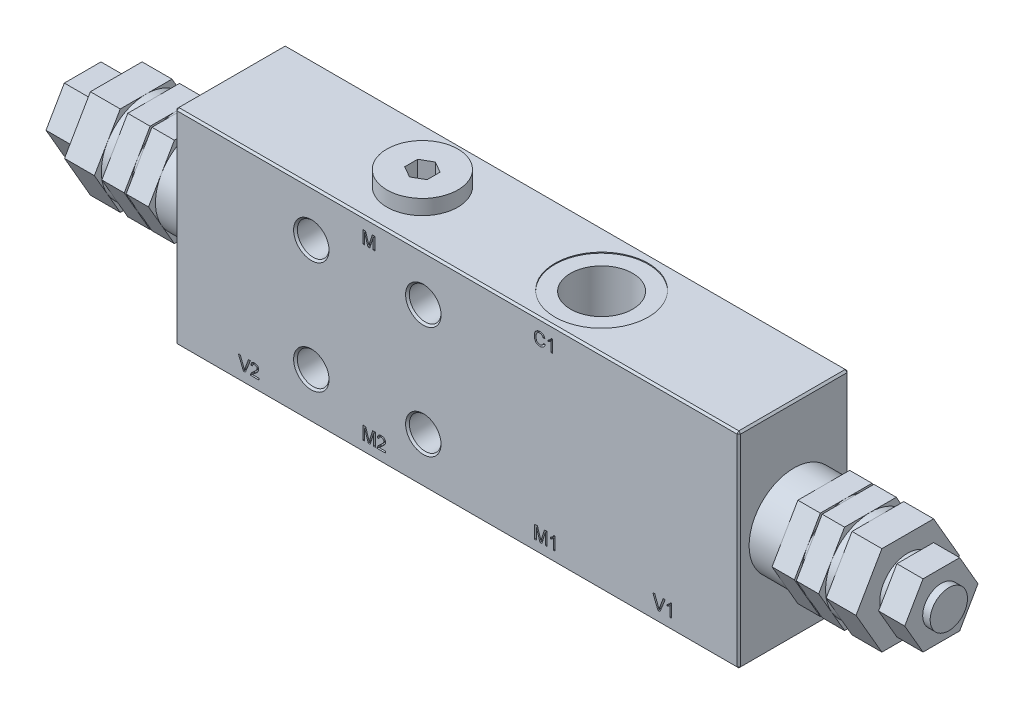
SolidWorks part; units mm, degrees
ref_plane "Front" through (0, 0, 0) normal (0, 0, 1) x (1, 0, 0)
ref_plane "Top" through (0, 0, 0) normal (0, 1, 0) x (1, 0, 0)
ref_plane "Right" through (0, 0, 0) normal (1, 0, 0) x (0, 0, -1)
sketch "Sketch1" plane through (0, 0, 0) normal (0, 0, 1) x (1, 0, 0)
  line L0 (0, 0) -> (151, 0)
  line L1 (0, 0) -> (0, 55)
  line L2 (151, 55) -> (0, 55)
  line L3 (151, 55) -> (151, 0)
  circle A0 centre (36.5, 42.5) radius 4.25
  circle A1 centre (66.5, 42.5) radius 4.25
  circle A2 centre (36.5, 12.5) radius 4.25
  circle A3 centre (66.5, 12.5) radius 4.25
  dimension "D6" = 8.5
  dimension "D1" = 55
  dimension "D2" = 12.5
  dimension "D3" = 30
  dimension "D4" = 30
  dimension "D5" = 36.5
  dimension "D7" = 151
extrude "Base-Extrude" add sketch "Sketch1" against normal blind 29.5
chamfer "Chamfer1" distance 0.5 angle 45 20 edges at (151, 27.5, -29.5) (40.75, 42.5, -29.5) (40.75, 42.5, 0) (75.5, 0, -29.5) (70.75, 42.5, -29.5) (70.75, 42.5, 0) (40.75, 12.5, -29.5) (40.75, 12.5, 0) (70.75, 12.5, -29.5) (70.75, 12.5, 0) (0, 27.5, -29.5) (75.5, 0, 0) (151, 27.5, 0) (75.5, 55, 0) (0, 27.5, 0) (75.5, 55, -29.5) (0, 0, -14.75) (151, 0, -14.75) (151, 55, -14.75) (0, 55, -14.75)
sketch "Sketch5" plane through (0, 0, -29.5) normal (0, 0, -1) x (-1, 0, 0)
  line L0 (0, 0) -> (0, 55) construction
  line L1 (0, 0) -> (-151, 0) construction
  circle A0 centre (-51.5, 27.5) radius 4.5
  dimension "D2" = 9
  dimension "D1" = 51.5
  dimension "D3" = 27.5
extrude "Cut-Extrude4" cut sketch "Sketch5" against normal blind 20
hole_wizard "Hole1" positions "Sketch7" profile "Sketch6" legacy
sketch "Sketch7" plane through (0, 55, 0) normal (0, 1, 0) x (-1, 0, 0)
  line L0 (-151, -29) -> (-151, -0.5) construction
  line L1 (-0.5, -29.5) -> (-150.5, -29.5) construction
  point P0 (-99.5, -14.75)
  dimension "D1" = 51.5
  dimension "D2" = 14.75
sketch "Sketch6" plane through (99.5, 55, -14.75) normal (1, 0, 0) x (0, 0, 1)
  line L0 (0, 0) -> (0, 20)
  line L1 (0, 20) -> (8.331, 20)
  line L2 (8.331, 20) -> (8.331, 0.25)
  line L3 (8.331, 0.25) -> (12.5, 0.25)
  line L4 (12.5, 0.25) -> (12.5, 0)
  line L5 (12.5, 0) -> (0, 0)
  line L6 (0, 110) -> (0, -10) construction
  dimension "Diameter" = 16.662
  dimension "Depth" = 20
  dimension "C-Bore Diameter" = 25
  dimension "C-Bore Depth" = 0.25
sketch "Sketch8" plane through (0, 55, 0) normal (0, 1, 0) x (-1, 0, 0)
  line L3 (-0.5, -29.5) -> (-150.5, -29.5) construction
  circle A0 centre (-51.5, -14.75) radius 9.5
  circle A1 centre (-99.5, -14.75) radius 8.331 construction
  dimension "D1" = 48
  dimension "D2" = 19
  dimension "D3" = 14.75
extrude "Boss-Extrude1" add sketch "Sketch8" along normal blind 4
sketch "Sketch9" plane through (0, 59, 0) normal (0, 1, 0) x (-1, 0, 0)
  line L1 (-51.5, -18.2141) -> (-48.5, -16.4821)
  line L2 (-48.5, -16.4821) -> (-48.5, -13.0179)
  line L3 (-48.5, -13.0179) -> (-51.5, -11.2859)
  line L4 (-51.5, -11.2859) -> (-54.5, -13.0179)
  line L5 (-54.5, -13.0179) -> (-54.5, -16.4821)
  line L6 (-54.5, -16.4821) -> (-51.5, -18.2141)
  circle A0 centre (-51.5, -14.75) radius 3 construction
  circle A1 centre (-51.5, -14.75) radius 9.5 construction
  dimension "D1" = 6
extrude "Cut-Extrude5" cut sketch "Sketch9" against normal blind 10
hole_wizard "Hole2" positions "Sketch12" profile "Sketch11" legacy
sketch "Sketch12" plane through (0, 0, 0) normal (0, -1, 0) x (1, 0, 0)
  line L0 (0.5, 0) -> (150.5, 0) construction
  line L1 (151, -0.5) -> (151, -29) construction
  point P0 (131, -14.75)
  dimension "D1" = 14.75
  dimension "D2" = 20
sketch "Sketch11" plane through (131, 0, -14.75) normal (1, 0, 0) x (0, 0, -1)
  line L0 (0, 0) -> (0, 20)
  line L1 (0, 20) -> (8.331, 20)
  line L2 (8.331, 20) -> (8.331, 0.25)
  line L3 (8.331, 0.25) -> (12.5, 0.25)
  line L4 (12.5, 0.25) -> (12.5, 0)
  line L5 (12.5, 0) -> (0, 0)
  line L6 (0, 110) -> (0, -10) construction
  dimension "Diameter" = 16.662
  dimension "Depth" = 20
  dimension "C-Bore Diameter" = 25
  dimension "C-Bore Depth" = 0.25
pattern_linear "LPattern1" count 2 spacing 111 along (-1, 0, 0) of "Hole2"
sketch "Sketch13" plane through (0, 0, 0) normal (0, -1, 0) x (1, 0, 0)
  line L2 (151, -0.5) -> (151, -29) construction
  line L3 (0.5, -29.5) -> (150.5, -29.5) construction
  circle A0 centre (98, -14.75) radius 9.5
  circle A1 centre (52, -14.75) radius 9.5 construction
  dimension "D1" = 19
  dimension "D2" = 53
  dimension "D3" = 46
  dimension "D4" = 14.75
extrude "Boss-Extrude2" add sketch "Sketch13" along normal blind 4
sketch "Sketch14" plane through (0, -4, 0) normal (0, -1, 0) x (1, 0, 0)
  line L1 (98, -11.2859) -> (95, -13.0179)
  line L2 (95, -13.0179) -> (95, -16.4821)
  line L3 (95, -16.4821) -> (98, -18.2141)
  line L4 (98, -18.2141) -> (101, -16.4821)
  line L5 (101, -16.4821) -> (101, -13.0179)
  line L6 (101, -13.0179) -> (98, -11.2859)
  line L8 (52, -11.2859) -> (49, -13.0179) construction
  line L9 (49, -13.0179) -> (49, -16.4821) construction
  line L10 (49, -16.4821) -> (52, -18.2141) construction
  line L11 (52, -18.2141) -> (55, -16.4821) construction
  line L12 (55, -16.4821) -> (55, -13.0179) construction
  line L13 (55, -13.0179) -> (52, -11.2859) construction
  circle A0 centre (98, -14.75) radius 3 construction
  circle A1 centre (52, -14.75) radius 3 construction
  circle A3 centre (98, -14.75) radius 9.5 construction
  dimension "D1" = 6
  dimension "D2" = 6
extrude "Cut-Extrude6" cut sketch "Sketch14" against normal blind 10
sketch "Sketch43" plane through (0, 0, 0) normal (0, -1, 0) x (1, 0, 0)
  circle A0 centre (52, -14.75) radius 9.5 construction
  circle A1 centre (52, -14.75) radius 9.5
extrude "Extrude1" add sketch "Sketch43" along normal up to surface (4 mm away) up to face at (98, -4, -14.75)
sketch "Sketch44" plane through (0, -4, 0) normal (0, -1, 0) x (1, 0, 0)
  line L0 (49, -13.0179) -> (49, -16.4821) construction
  line L1 (49, -16.4821) -> (52, -18.2141) construction
  line L2 (52, -18.2141) -> (55, -16.4821) construction
  line L3 (55, -16.4821) -> (55, -13.0179) construction
  line L4 (55, -13.0179) -> (52, -11.2859) construction
  line L5 (52, -11.2859) -> (49, -13.0179) construction
  line L6 (49, -13.0179) -> (49, -16.4821)
  line L7 (49, -16.4821) -> (52, -18.2141)
  line L8 (52, -18.2141) -> (55, -16.4821)
  line L9 (55, -16.4821) -> (55, -13.0179)
  line L10 (55, -13.0179) -> (52, -11.2859)
  line L11 (52, -11.2859) -> (49, -13.0179)
extrude "Cut-Extrude13" cut sketch "Sketch44" against normal up to surface (10 mm away) up to face at (98, 6, -14.75)
sketch "Sketch15" plane through (151, 0, 0) normal (1, 0, 0) x (0, 0, -1)
  line L0 (9.5, 27.5) -> (29.5, 27.5) construction
  line L3 (0, 0.5) -> (0, 54.5) construction
  circle A0 centre (14.75, 27.5) radius 12
  dimension "D1" = 24
  dimension "D2" = 14.75
extrude "Boss-Extrude3" add sketch "Sketch15" along normal blind 8
sketch "Sketch16" plane through (159, 0, 0) normal (1, 0, 0) x (0, 0, -1)
  line L0 (9.5, 27.5) -> (29.5, 27.5) construction
  line L1 (21.6782, 39.5) -> (7.8218, 39.5)
  line L2 (7.8218, 39.5) -> (0.8936, 27.5)
  line L3 (0.8936, 27.5) -> (7.8218, 15.5)
  line L4 (7.8218, 15.5) -> (21.6782, 15.5)
  line L5 (21.6782, 15.5) -> (28.6064, 27.5)
  line L6 (28.6064, 27.5) -> (21.6782, 39.5)
  circle A0 centre (14.75, 27.5) radius 12 construction
  circle A1 centre (14.75, 27.5) radius 12 construction
  dimension "D1" = 24
extrude "Boss-Extrude4" add sketch "Sketch16" along normal blind 6
sketch "Sketch17" plane through (165, 0, 0) normal (1, 0, 0) x (0, 0, -1)
  circle A0 centre (14.75, 27.5) radius 12
  circle A1 centre (14.75, 27.5) radius 12 construction
  dimension "D1" = 24
extrude "Boss-Extrude5" add sketch "Sketch17" along normal blind 0.5
sketch "Sketch18" plane through (165.5, 0, 0) normal (1, 0, 0) x (0, 0, -1)
  line L0 (9.5, 27.5) -> (29.5, 27.5) construction
  line L1 (0.8936, 27.5) -> (7.8218, 15.5)
  line L2 (7.8218, 15.5) -> (21.6782, 15.5)
  line L3 (21.6782, 15.5) -> (28.6064, 27.5)
  line L4 (28.6064, 27.5) -> (21.6782, 39.5)
  line L5 (21.6782, 39.5) -> (7.8218, 39.5)
  line L6 (7.8218, 39.5) -> (0.8936, 27.5)
  circle A0 centre (14.75, 27.5) radius 12 construction
  circle A1 centre (14.75, 27.5) radius 12 construction
  dimension "D1" = 24
extrude "Boss-Extrude6" add sketch "Sketch18" along normal blind 6
sketch "Sketch19" plane through (171.5, 0, 0) normal (1, 0, 0) x (0, 0, -1)
  circle A0 centre (14.75, 27.5) radius 12
  dimension "D1" = 24
extrude "Boss-Extrude7" add sketch "Sketch19" along normal blind 2
sketch "Sketch20" plane through (173.5, 0, 0) normal (1, 0, 0) x (0, 0, -1)
  line L1 (0.8936, 27.5) -> (7.8218, 15.5)
  line L2 (7.8218, 15.5) -> (21.6782, 15.5)
  line L3 (21.6782, 15.5) -> (28.6064, 27.5)
  line L4 (28.6064, 27.5) -> (21.6782, 39.5)
  line L5 (21.6782, 39.5) -> (7.8218, 39.5)
  line L6 (7.8218, 39.5) -> (0.8936, 27.5)
  circle A0 centre (14.75, 27.5) radius 12 construction
  dimension "D1" = 24
extrude "Boss-Extrude8" add sketch "Sketch20" along normal blind 8
sketch "Sketch21" plane through (181.5, 0, 0) normal (1, 0, 0) x (0, 0, -1)
  circle A0 centre (14.75, 27.5) radius 7.5
  dimension "D1" = 15
extrude "Boss-Extrude9" add sketch "Sketch21" along normal blind 2
sketch "Sketch22" plane through (183.5, 0, 0) normal (1, 0, 0) x (0, 0, -1)
  line L1 (4.935, 27.5) -> (9.8425, 19)
  line L2 (9.8425, 19) -> (19.6575, 19)
  line L3 (19.6575, 19) -> (24.565, 27.5)
  line L4 (24.565, 27.5) -> (19.6575, 36)
  line L5 (19.6575, 36) -> (9.8425, 36)
  line L6 (9.8425, 36) -> (4.935, 27.5)
  circle A0 centre (14.75, 27.5) radius 8.5 construction
  dimension "D1" = 17
extrude "Boss-Extrude10" add sketch "Sketch22" along normal blind 7
sketch "Sketch23" plane through (190.5, 0, 0) normal (1, 0, 0) x (0, 0, -1)
  circle A0 centre (14.75, 27.5) radius 5
  dimension "D1" = 10
extrude "Boss-Extrude11" add sketch "Sketch23" along normal blind 2
sketch "Sketch24" plane through (0, 0, 0) normal (-1, 0, 0) x (0, 0, 1)
  line L0 (-9.5, 27.5) -> (-29.5, 27.5) construction
  line L1 (0, 54.5) -> (0, 0.5) construction
  circle A0 centre (-14.75, 27.5) radius 12
  dimension "D1" = 24
  dimension "D2" = 14.75
extrude "Boss-Extrude12" add sketch "Sketch24" along normal blind 8
sketch "Sketch25" plane through (-8, 0, 0) normal (-1, 0, 0) x (0, 0, 1)
  line L0 (-9.5, 27.5) -> (-29.5, 27.5) construction
  line L1 (-0.8936, 27.5) -> (-7.8218, 39.5)
  line L2 (-7.8218, 39.5) -> (-21.6782, 39.5)
  line L3 (-21.6782, 39.5) -> (-28.6064, 27.5)
  line L4 (-28.6064, 27.5) -> (-21.6782, 15.5)
  line L5 (-21.6782, 15.5) -> (-7.8218, 15.5)
  line L6 (-7.8218, 15.5) -> (-0.8936, 27.5)
  circle A0 centre (-14.75, 27.5) radius 12 construction
  circle A1 centre (-14.75, 27.5) radius 12 construction
  dimension "D1" = 24
extrude "Boss-Extrude13" add sketch "Sketch25" along normal blind 6
sketch "Sketch26" plane through (-14, 0, 0) normal (-1, 0, 0) x (0, 0, 1)
  circle A0 centre (-14.75, 27.5) radius 12
  dimension "D1" = 24
extrude "Boss-Extrude14" add sketch "Sketch26" along normal blind 0.5
sketch "Sketch27" plane through (-14.5, 0, 0) normal (-1, 0, 0) x (0, 0, 1)
  line L1 (-0.8936, 27.5) -> (-7.8218, 39.5)
  line L2 (-7.8218, 39.5) -> (-21.6782, 39.5)
  line L3 (-21.6782, 39.5) -> (-28.6064, 27.5)
  line L4 (-28.6064, 27.5) -> (-21.6782, 15.5)
  line L5 (-21.6782, 15.5) -> (-7.8218, 15.5)
  line L6 (-7.8218, 15.5) -> (-0.8936, 27.5)
  circle A0 centre (-14.75, 27.5) radius 12 construction
  dimension "D1" = 24
extrude "Boss-Extrude15" add sketch "Sketch27" along normal blind 6
sketch "Sketch28" plane through (-20.5, 0, 0) normal (-1, 0, 0) x (0, 0, 1)
  line L0 (-9.5, 27.5) -> (-29.5, 27.5) construction
  circle A0 centre (-14.75, 27.5) radius 12
  circle A1 centre (-14.75, 27.5) radius 12 construction
  dimension "D1" = 24
extrude "Boss-Extrude16" add sketch "Sketch28" along normal blind 2
sketch "Sketch29" plane through (-22.5, 0, 0) normal (-1, 0, 0) x (0, 0, 1)
  line L1 (-0.8936, 27.5) -> (-7.8218, 39.5)
  line L2 (-7.8218, 39.5) -> (-21.6782, 39.5)
  line L3 (-21.6782, 39.5) -> (-28.6064, 27.5)
  line L4 (-28.6064, 27.5) -> (-21.6782, 15.5)
  line L5 (-21.6782, 15.5) -> (-7.8218, 15.5)
  line L6 (-7.8218, 15.5) -> (-0.8936, 27.5)
  circle A0 centre (-14.75, 27.5) radius 12 construction
  dimension "D1" = 24
extrude "Boss-Extrude17" add sketch "Sketch29" along normal blind 8
sketch "Sketch30" plane through (-30.5, 0, 0) normal (-1, 0, 0) x (0, 0, 1)
  circle A0 centre (-14.75, 27.5) radius 7.5
  dimension "D1" = 15
extrude "Boss-Extrude18" add sketch "Sketch30" along normal blind 2
sketch "Sketch31" plane through (-32.5, 0, 0) normal (-1, 0, 0) x (0, 0, 1)
  line L1 (-4.935, 27.5) -> (-9.8425, 36)
  line L2 (-9.8425, 36) -> (-19.6575, 36)
  line L3 (-19.6575, 36) -> (-24.565, 27.5)
  line L4 (-24.565, 27.5) -> (-19.6575, 19)
  line L5 (-19.6575, 19) -> (-9.8425, 19)
  line L6 (-9.8425, 19) -> (-4.935, 27.5)
  circle A0 centre (-14.75, 27.5) radius 8.5 construction
  dimension "D1" = 17
extrude "Boss-Extrude19" add sketch "Sketch31" along normal blind 7
sketch "Sketch32" plane through (-39.5, 0, 0) normal (-1, 0, 0) x (0, 0, 1)
  line L0 (-14.75, 54.75) -> (-14.75, 55) construction
  circle A0 centre (-14.75, 27.5) radius 5
  circle A2 centre (-14.75, 27.5) radius 12 construction
  dimension "D1" = 10
extrude "Boss-Extrude20" add sketch "Sketch32" along normal blind 2
sketch "Sketch33" plane through (0, 0, 0) normal (0, 0, 1) x (1, 0, 0)
  line L0 (150.5, 0) -> (0.5, 0) construction
  line L1 (151, 54.5) -> (151, 0.5) construction
  text T0 "V1" font "Arial" height 3.5
  dimension "D1" = 3
  dimension "D2" = 23
extrude "Cut-Extrude7" cut sketch "Sketch33" against normal blind 1
sketch "Sketch34" plane through (0, 0, 0) normal (0, 0, 1) x (1, 0, 0)
  line L0 (0, 0.5) -> (0, 54.5) construction
  line L1 (150.5, 0) -> (0.5, 0) construction
  text T0 "V2" font "Arial" height 3.5
  dimension "D1" = 17
  dimension "D2" = 3
extrude "Cut-Extrude8" cut sketch "Sketch34" against normal blind 1
sketch "Sketch35" plane through (0, 0, 0) normal (0, 0, 1) x (1, 0, 0)
  line L1 (151, 54.5) -> (151, 0.5) construction
  line L2 (0.5, 55) -> (150.5, 55) construction
  text T0 "C1" font "Arial" height 3.5
  dimension "D1" = 55
  dimension "D2" = 6.5
extrude "Cut-Extrude9" cut sketch "Sketch35" against normal blind 1
sketch "Sketch36" plane through (0, 0, 0) normal (0, 0, 1) x (1, 0, 0)
  line L0 (0.5, 55) -> (150.5, 55) construction
  line L1 (0, 0.5) -> (0, 54.5) construction
  text T0 "M" font "Arial" height 3.5
  dimension "D1" = 6.5
  dimension "D2" = 50
extrude "Cut-Extrude10" cut sketch "Sketch36" against normal blind 1
sketch "Sketch37" plane through (0, 0, 0) normal (0, 0, 1) x (1, 0, 0)
  line L0 (150.5, 0) -> (0.5, 0) construction
  line L1 (0, 0.5) -> (0, 54.5) construction
  text T0 "M2" font "Arial" height 3.5
  dimension "D1" = 3
  dimension "D2" = 50
extrude "Cut-Extrude11" cut sketch "Sketch37" against normal blind 1
sketch "Sketch38" plane through (0, 0, 0) normal (0, 0, 1) x (1, 0, 0)
  line L0 (150.5, 0) -> (0.5, 0) construction
  line L1 (151, 54.5) -> (151, 0.5) construction
  text T0 "M1" font "Arial" height 3.5
  dimension "D1" = 3
  dimension "D2" = 55
extrude "Cut-Extrude12" cut sketch "Sketch38" against normal blind 1
hole_wizard "Hole3" [suppressed] positions "Sketch40" profile "Sketch39" legacy
sketch "Sketch40" plane through (0, 55, 0) normal (0, 1, 0) x (-1, 0, 0)
  line L0 (-150.5, 0) -> (-0.5, 0) construction
  circle A0 centre (-99.5, -14.75) radius 8.331 construction
  point P0 (-51.5, -14.75)
  dimension "D2" = 48
  dimension "D1" = 14.75
sketch "Sketch39" plane through (51.5, 55, -14.75) normal (1, 0, 0) x (0, 0, 1)
  line L0 (0, 0) -> (0, 20)
  line L1 (0, 20) -> (6.5785, 20)
  line L2 (6.5785, 20) -> (6.5785, 0.25)
  line L3 (6.5785, 0.25) -> (11, 0.25)
  line L4 (11, 0.25) -> (11, 0)
  line L5 (11, 0) -> (0, 0)
  line L6 (0, 110) -> (0, -10) construction
  dimension "Diameter" = 13.157
  dimension "Depth" = 20
  dimension "C-Bore Diameter" = 22
  dimension "C-Bore Depth" = 0.25
hole_wizard "Hole4" [suppressed] positions "Sketch42" profile "Sketch41" legacy
sketch "Sketch42" plane through (0, 0, 0) normal (0, -1, 0) x (1, 0, 0)
  line L0 (0.5, 0) -> (150.5, 0) construction
  line L1 (151, -0.5) -> (151, -29) construction
  point P0 (52, -14.75)
  dimension "D1" = 14.75
  dimension "D2" = 53
sketch "Sketch41" plane through (52, 0, -14.75) normal (1, 0, 0) x (0, 0, -1)
  line L0 (0, 0) -> (0, 20)
  line L1 (0, 20) -> (6.5785, 20)
  line L2 (6.5785, 20) -> (6.5785, 0.25)
  line L3 (6.5785, 0.25) -> (11, 0.25)
  line L4 (11, 0.25) -> (11, 0)
  line L5 (11, 0) -> (0, 0)
  line L6 (0, 110) -> (0, -10) construction
  dimension "Diameter" = 13.157
  dimension "Depth" = 20
  dimension "C-Bore Diameter" = 22
  dimension "C-Bore Depth" = 0.25
pattern_linear "LPattern2" [suppressed] count 2 spacing 46
